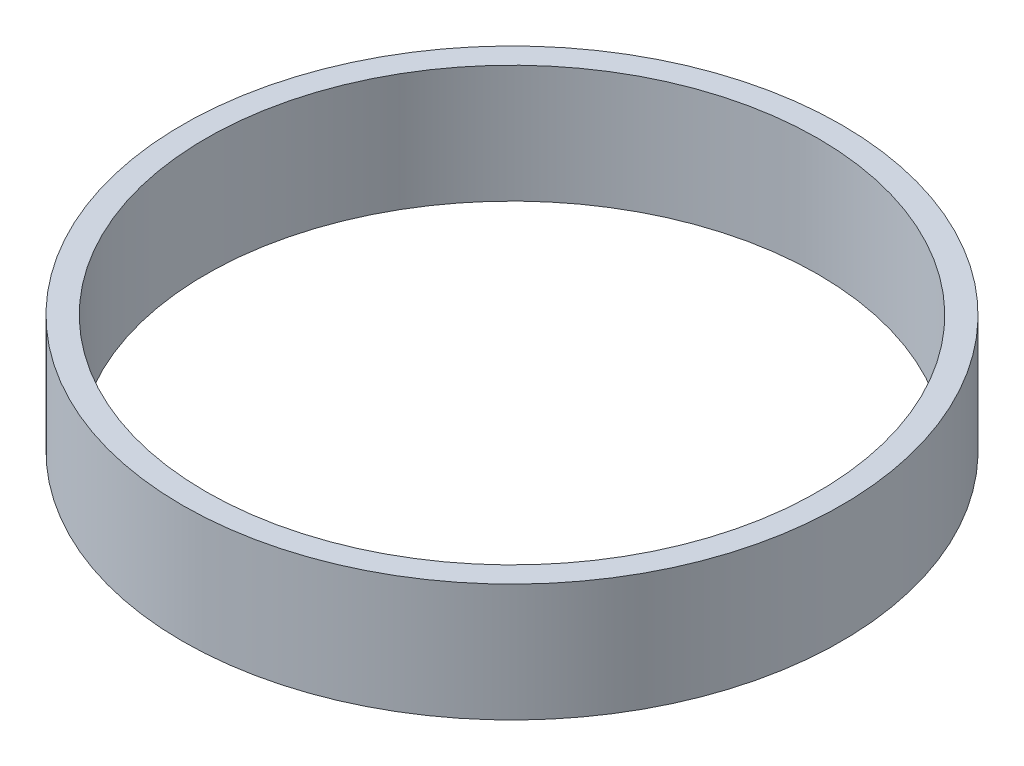
SolidWorks part; units mm, degrees
material "Plain Carbon Steel"
ref_plane "Front Plane" through (0, 0, 0) normal (0, 0, 1) x (1, 0, 0)
ref_plane "Top Plane" through (0, 0, 0) normal (0, 1, 0) x (1, 0, 0)
ref_plane "Right Plane" through (0, 0, 0) normal (1, 0, 0) x (0, 0, -1)
sketch "Sketch1" plane through (0, 0, 0) normal (0, 1, 0) x (1, 0, 0)
  circle A0 centre (0, 0) radius 35
  circle A1 centre (0, 0) radius 32.5
  dimension "D1" = 65
  dimension "D2" = 70
extrude "Boss-Extrude1" add sketch "Sketch1" along normal blind 12.5
